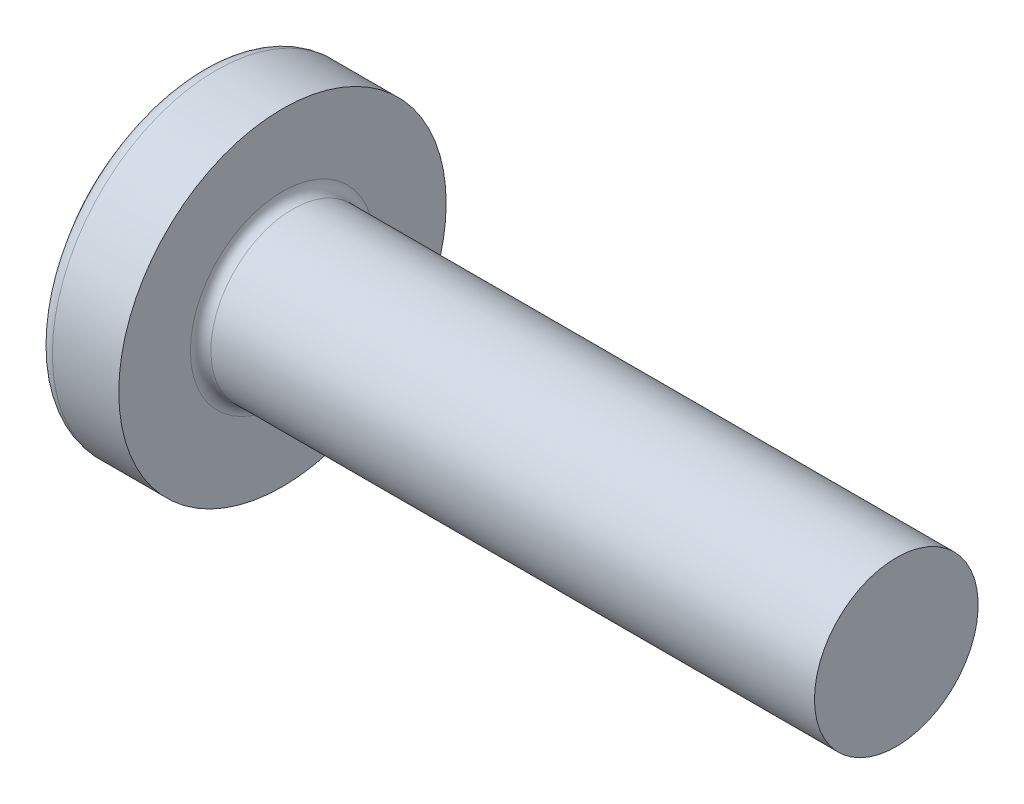
SolidWorks part; units mm, degrees
material "ABS"
ref_plane "Plane1" through (0, 0, 0) normal (0, 0, 1) x (1, 0, 0)
ref_plane "Plane2" through (0, 0, 0) normal (0, 1, 0) x (1, 0, 0)
ref_plane "Plane3" through (0, 0, 0) normal (1, 0, 0) x (0, 0, -1)
sketch "BodySke" plane through (0, 0, 0) normal (0, 0, 1) x (1, 0, 0)
  line L0 (1.3, 0.8) -> (1.3, 1.6)
  line L1 (1.475, 6.35) -> (1.475, -3.175) construction
  line L2 (-25.4, 0) -> (127, 0) construction
  line L3 (7.3, 0) -> (0, 0)
  line L4 (1.3, 0.8) -> (7.3, 0.8)
  line L5 (7.3, 0.8) -> (7.3, 0)
  line L6 (0.6507, 1.6) -> (1.3, 1.6)
  line L8 (1.3, 6.35) -> (1.3, -3.175) construction
  arc A0 (0.5326, 1.5426) -> (0, 0) centre (2.5, 0) ccw
  arc A2 (0.5326, 1.5426) -> (0.6507, 1.6) centre (0.6507, 1.45) cw
  dimension "Head_crown_rad" = 2.5
  dimension "Head_fillet_rad" = 0.15
  dimension "Length" = 6
  dimension "Head_ht" = 1.3
  dimension "Head_dia" = 3.2
  dimension "Advance" = 0.35
  dimension "Thread_nom" = 6
  dimension "Diameter" = 1.6
revolve "Base-Revolve" add sketch "BodySke"
cosmetic thread "ThreadCosmetic" [suppressed]
fillet "Fillet1" radius 0.1 1 edges at (1.3, 0, 0.8)
sketch "Sketch3" plane through (0, 0, 0) normal (1, 0, 0) x (0, 0, -1)
  line L0 (0.24, -0.8) -> (-0.24, -0.8)
  line L1 (0.24, -0.8) -> (0.24, 0.8)
  line L2 (-0.24, 0.8) -> (0.24, 0.8)
  line L3 (-0.24, 0.8) -> (-0.24, -0.8)
  dimension "Cross_dia" = 1.6
  dimension "D1" = 0.8
  dimension "Cross_width" = 0.48
  dimension "D2" = 0.24
ref_plane "Plane4" through (0.9, 0, 0) normal (1, 0, 0) x (0, 0, -1)
sketch "Sketch4" plane through (0.9, 0, 0) normal (1, 0, 0) x (0, 0, -1)
  line L0 (0.24, -0.3513) -> (-0.24, -0.3513)
  line L1 (0.24, -0.3513) -> (0.24, 0.3513)
  line L2 (-0.24, 0.3513) -> (0.24, 0.3513)
  line L3 (-0.24, 0.3513) -> (-0.24, -0.3513)
  dimension "D1" = 0.48
  dimension "D2" = 0.7026
  dimension "D3" = 0.24
  dimension "D4" = 0.3513
loft "Recess" cut profiles "Sketch3", "Sketch4"
pattern_circular "RecPat" count 2 every 90 about axis through (0, 0, 0) along (1, 0, 0) of "Recess"
sketch "RecCorSke" plane through (0, 0, 0) normal (0, 0, 1) x (1, 0, 0)
  line L0 (-3.175, 0) -> (15.875, 0) construction
  line L1 (-25.4, 0) -> (127, 0) construction
  line L2 (0, 0) -> (0, 0.4184)
  line L3 (0, 0.4184) -> (0.9, 0.3555)
  line L4 (0.9, 0.3555) -> (1.0155, 0)
  line L5 (1.0155, 0) -> (0, 0)
  dimension "Diameter" = 0.711
  dimension "Depth" = 0.9
  dimension "Draft_angle" = 4
  dimension "Bottom_angle" = 18
revolve "RecessCore" cut sketch "RecCorSke" angle 360 about L0
sketch "ThdSchSke" plane through (0, 0, 0) normal (0, 0, 1) x (1, 0, 0)
  line L0 (2, -0.601) -> (1.8607, -0.8)
  line L1 (2, -0.601) -> (2.1393, -0.8)
  line L2 (2.1393, -0.8) -> (2.1393, -1)
  line L3 (-3.175, 0) -> (5.1513, 0) construction
  line L5 (2.1393, -1) -> (1.8607, -1)
  line L6 (1.8607, -1) -> (1.8607, -0.8)
  dimension "Diameter" = 1.6
  dimension "SideAngle" = 55
  dimension "VeeAngle" = 70
  dimension "Thread_minor" = 1.202
  dimension "Overcut" = 2
  dimension "Start" = 2
revolve "ThreadSchematic" [suppressed] cut sketch "ThdSchSke" angle 360 about L3
pattern_linear "ThdSchPat" [suppressed]
equation "\"D1@Sketch3\" = \"Cross_dia@Sketch3\" / 2"
equation "\"D2@Sketch3\" = \"Cross_width@Sketch3\" / 2"
equation "\"Depth@RecCorSke\" = \"Cross_depth@Plane4\""
equation "\"D1@Sketch4\" = \"Cross_width@Sketch3\""
equation "\"D2@Sketch4\" = \"Cross_dia@Sketch3\" - 2.0 * \"Cross_depth@Plane4\" * tan(26.5  * 0.017453292)"
equation "\"D3@Sketch4\" = \"D1@Sketch4\" / 2"
equation "\"D4@Sketch4\" = \"D2@Sketch4\" / 2"
equation "\"Thread_length@ThreadCosmetic\" = ((sgn( (\"Length@BodySke\" - \"Advance@BodySke\" * 2.0 ) - \"Thread_nom@BodySke\" )-1)*( (\"Length@BodySke\" - \"Advance@BodySke\" * 2.0 ) - \"Thread_nom@BodySke\" ))/-2+ \"Thread_nom@BodySke\""
equation "\"Thread_minor@ThdSchSke\" = \"Thread_minor@ThreadCosmetic\""
equation "\"Diameter@ThdSchSke\" = \"Diameter@BodySke\""
equation "\"Overcut@ThdSchSke\" = \"Diameter@BodySke\" * 1.25"
equation "\"Start@ThdSchSke\" = \"Head_ht@BodySke\" + \"Length@BodySke\" - \"Thread_length@ThreadCosmetic\"  '---Non-countersunk---"
equation "\"Num_threads@ThdSchPat\" = int( \"Thread_length@ThreadCosmetic\" / \"Advance@BodySke\" + 0.999 )  + 1"
equation "\"Advance@ThdSchPat\" = \"Thread_length@ThreadCosmetic\" /  (\"Num_threads@ThdSchPat\" - 1) 'relax it"
